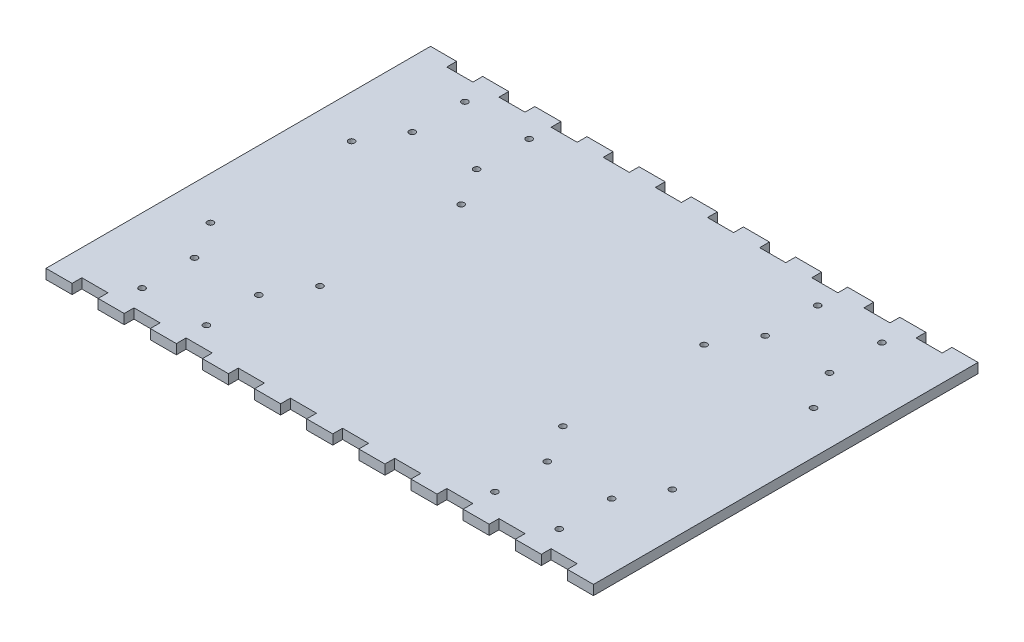
SolidWorks part; units mm, degrees
ref_plane "Front Plane" through (0, 0, 0) normal (0, 0, 1) x (1, 0, 0)
ref_plane "Top Plane" through (0, 0, 0) normal (0, 1, 0) x (1, 0, 0)
ref_plane "Right Plane" through (0, 0, 0) normal (1, 0, 0) x (0, 0, -1)
sketch "Sketch2" plane through (0, 0, 0) normal (0, 1, 0) x (1, 0, 0)
  line L11 (25.4, 88.9) -> (25.4, 93.6625)
  line L12 (12.7, -88.9) -> (25.4, -88.9)
  line L23 (0, -88.9) -> (0, 88.9)
  line L24 (12.7, 88.9) -> (25.4, 88.9)
  line L29 (266.7, -88.9) -> (266.7, 88.9)
  line L30 (25.4, 93.6625) -> (38.1, 93.6625)
  line L35 (38.1, 88.9) -> (38.1, 93.6625)
  line L41 (0, 88.9) -> (0, 93.6625)
  line L42 (0, 93.6625) -> (12.7, 93.6625)
  line L47 (12.7, 88.9) -> (12.7, 93.6625)
  line L48 (50.8, 88.9) -> (50.8, 93.6625)
  line L53 (50.8, 93.6625) -> (63.5, 93.6625)
  line L54 (63.5, 88.9) -> (63.5, 93.6625)
  line L59 (76.2, 88.9) -> (76.2, 93.6625)
  line L60 (76.2, 93.6625) -> (88.9, 93.6625)
  line L65 (88.9, 88.9) -> (88.9, 93.6625)
  line L66 (101.6, 88.9) -> (101.6, 93.6625)
  line L71 (101.6, 93.6625) -> (114.3, 93.6625)
  line L72 (114.3, 88.9) -> (114.3, 93.6625)
  line L77 (127, 88.9) -> (127, 93.6625)
  line L78 (127, 93.6625) -> (139.7, 93.6625)
  line L79 (139.7, 88.9) -> (139.7, 93.6625)
  line L80 (152.4, 88.9) -> (152.4, 93.6625)
  line L81 (152.4, 93.6625) -> (165.1, 93.6625)
  line L82 (165.1, 88.9) -> (165.1, 93.6625)
  line L83 (177.8, 88.9) -> (177.8, 93.6625)
  line L84 (177.8, 93.6625) -> (190.5, 93.6625)
  line L85 (190.5, 88.9) -> (190.5, 93.6625)
  line L86 (203.2, 88.9) -> (203.2, 93.6625)
  line L87 (203.2, 93.6625) -> (215.9, 93.6625)
  line L88 (215.9, 88.9) -> (215.9, 93.6625)
  line L89 (228.6, 88.9) -> (228.6, 93.6625)
  line L90 (228.6, 93.6625) -> (241.3, 93.6625)
  line L91 (241.3, 88.9) -> (241.3, 93.6625)
  line L92 (254, 88.9) -> (254, 93.6625)
  line L93 (254, 93.6625) -> (266.7, 93.6625)
  line L94 (266.7, 88.9) -> (266.7, 93.6625)
  line L95 (38.1, 88.9) -> (50.8, 88.9)
  line L96 (63.5, 88.9) -> (76.2, 88.9)
  line L97 (88.9, 88.9) -> (101.6, 88.9)
  line L98 (114.3, 88.9) -> (127, 88.9)
  line L99 (139.7, 88.9) -> (152.4, 88.9)
  line L100 (165.1, 88.9) -> (177.8, 88.9)
  line L101 (190.5, 88.9) -> (203.2, 88.9)
  line L102 (215.9, 88.9) -> (228.6, 88.9)
  line L103 (241.3, 88.9) -> (254, 88.9)
  line L104 (0, 0) -> (266.7, 0) construction
  line L105 (241.3, -88.9) -> (254, -88.9)
  line L106 (215.9, -88.9) -> (228.6, -88.9)
  line L107 (190.5, -88.9) -> (203.2, -88.9)
  line L108 (165.1, -88.9) -> (177.8, -88.9)
  line L109 (139.7, -88.9) -> (152.4, -88.9)
  line L110 (114.3, -88.9) -> (127, -88.9)
  line L111 (88.9, -88.9) -> (101.6, -88.9)
  line L112 (63.5, -88.9) -> (76.2, -88.9)
  line L113 (38.1, -88.9) -> (50.8, -88.9)
  line L114 (266.7, -88.9) -> (266.7, -93.6625)
  line L115 (254, -93.6625) -> (266.7, -93.6625)
  line L116 (254, -88.9) -> (254, -93.6625)
  line L117 (241.3, -88.9) -> (241.3, -93.6625)
  line L118 (228.6, -93.6625) -> (241.3, -93.6625)
  line L119 (228.6, -88.9) -> (228.6, -93.6625)
  line L120 (215.9, -88.9) -> (215.9, -93.6625)
  line L121 (203.2, -93.6625) -> (215.9, -93.6625)
  line L122 (203.2, -88.9) -> (203.2, -93.6625)
  line L123 (190.5, -88.9) -> (190.5, -93.6625)
  line L124 (177.8, -93.6625) -> (190.5, -93.6625)
  line L125 (177.8, -88.9) -> (177.8, -93.6625)
  line L126 (165.1, -88.9) -> (165.1, -93.6625)
  line L127 (152.4, -93.6625) -> (165.1, -93.6625)
  line L128 (152.4, -88.9) -> (152.4, -93.6625)
  line L129 (139.7, -88.9) -> (139.7, -93.6625)
  line L130 (127, -93.6625) -> (139.7, -93.6625)
  line L131 (127, -88.9) -> (127, -93.6625)
  line L132 (114.3, -88.9) -> (114.3, -93.6625)
  line L133 (101.6, -93.6625) -> (114.3, -93.6625)
  line L134 (101.6, -88.9) -> (101.6, -93.6625)
  line L135 (88.9, -88.9) -> (88.9, -93.6625)
  line L136 (76.2, -93.6625) -> (88.9, -93.6625)
  line L137 (76.2, -88.9) -> (76.2, -93.6625)
  line L138 (63.5, -88.9) -> (63.5, -93.6625)
  line L139 (50.8, -93.6625) -> (63.5, -93.6625)
  line L140 (50.8, -88.9) -> (50.8, -93.6625)
  line L141 (12.7, -88.9) -> (12.7, -93.6625)
  line L142 (0, -93.6625) -> (12.7, -93.6625)
  line L143 (0, -88.9) -> (0, -93.6625)
  line L144 (38.1, -88.9) -> (38.1, -93.6625)
  line L145 (25.4, -93.6625) -> (38.1, -93.6625)
  line L146 (12.7, -88.9) -> (25.4, -88.9)
  line L147 (25.4, -88.9) -> (25.4, -93.6625)
  line L148 (38.1, -88.9) -> (50.8, -88.9)
  line L149 (63.5, -88.9) -> (76.2, -88.9)
  line L150 (88.9, -88.9) -> (101.6, -88.9)
  line L151 (114.3, -88.9) -> (127, -88.9)
  line L152 (139.7, -88.9) -> (152.4, -88.9)
  line L153 (165.1, -88.9) -> (177.8, -88.9)
  line L154 (190.5, -88.9) -> (203.2, -88.9)
  line L155 (215.9, -88.9) -> (228.6, -88.9)
  line L156 (241.3, -88.9) -> (254, -88.9)
  dimension "D1" = 177.8
  dimension "D2" = 266.7
  dimension "D3" = 12.7
  dimension "D4" = 4.7625
extrude "Boss-Extrude1" add sketch "Sketch2" along normal blind 4.7625 contours L12 L147 L145 L144 L113 L140 L139 L138 L112 L137 L136 L135 L111 L134 L133 L132 L110 L131 L130 L129 L109 L128 L127 L126 L108 L125 L124 L123 L107 L122 L121 L120 L106 L119 L118 L117 L105 L116 L115 L114 L29 L94 L93 L92 L103 L91 L90 L89 L102 L88 L87 | L23 L104 L29 L94 L93 L92 L103 L91 L90 L89 L102 L88 L87 L86 L101 L85 L84 L83 L100 L82 L81 L80 L99 L79 L78 L77 L98 L72 L71 L66 L97 L65 L60 L59 L96 L54 L53 L48 L95 L35 L30 L11 L24 L47 L42 L41
sketch "Sketch5" plane through (0, 4.7625, 0) normal (0, 1, 0) x (1, 0, 0)
  line L1 (25.4, 93.6625) -> (38.1, 93.6625) construction
  line L3 (0, 93.6625) -> (12.7, 93.6625) construction
  line L5 (0, 0) -> (266.7, 0) construction
  line L6 (0, -93.6625) -> (0, 93.6625) construction
  line L7 (266.7, 93.6625) -> (266.7, -93.6625) construction
  circle A0 centre (31.75, 78.6125) radius 1.5
  circle A1 centre (63.07, 78.6125) radius 1.5
  circle A2 centre (63.07, 53.0625) radius 1.5
  circle A3 centre (31.75, 53.0625) radius 1.5
  circle A20 centre (203.63, 78.6125) radius 1.5
  circle A21 centre (203.63, 53.0625) radius 1.5
  circle A22 centre (234.95, 53.0625) radius 1.5
  circle A23 centre (234.95, 78.6125) radius 1.5
  circle A24 centre (234.95, -78.6125) radius 1.5
  circle A25 centre (234.95, -53.0625) radius 1.5
  circle A26 centre (203.63, -53.0625) radius 1.5
  circle A27 centre (203.63, -78.6125) radius 1.5
  circle A28 centre (31.75, -53.0625) radius 1.5
  circle A29 centre (63.07, -53.0625) radius 1.5
  circle A30 centre (63.07, -78.6125) radius 1.5
  circle A31 centre (31.75, -78.6125) radius 1.5
  circle A32 centre (20.83, 34.385) radius 1.5
  circle A33 centre (74.17, 34.385) radius 1.5
  circle A34 centre (192.53, 34.385) radius 1.5
  circle A35 centre (245.87, 34.385) radius 1.5
  circle A36 centre (245.87, -34.385) radius 1.5
  circle A37 centre (192.53, -34.385) radius 1.5
  circle A38 centre (74.17, -34.385) radius 1.5
  circle A39 centre (20.83, -34.385) radius 1.5
  point P3 (64.57, 78.6125)
  point P7 (30.25, 78.6125)
  point P23 (31.75, 93.6625)
  point P50 (31.75, 80.1125)
  point P51 (31.75, 51.5625)
  point P52 (0, 0)
  dimension "D1" = 28.55
  dimension "D3" = 3
  dimension "D4" = 2
  dimension "D2" = 13.55
  dimension "D5" = 34.32
  dimension "D6" = 31.75
  dimension "D7" = 20.83
  dimension "D8" = 53.34
  dimension "D9" = 59.2775
  dimension "D11" = 20.83
  dimension "D10" = 2
extrude "Cut-Extrude1" cut sketch "Sketch5" against normal through all
sketch "Sketch6" plane through (0, 4.7625, 0) normal (0, 1, 0) x (1, 0, 0)
  line L0 (0, -93.6625) -> (0, 93.6625) construction
  line L1 (0, 93.6625) -> (12.7, 93.6625) construction
  text T0 "TREY MADE THIS CHASSIS\r\n the robot will be on this\r\n<i>      -\"Danny Devito\"</i>"
  dimension "D1" = 101.6
  dimension "D2" = 82.677
